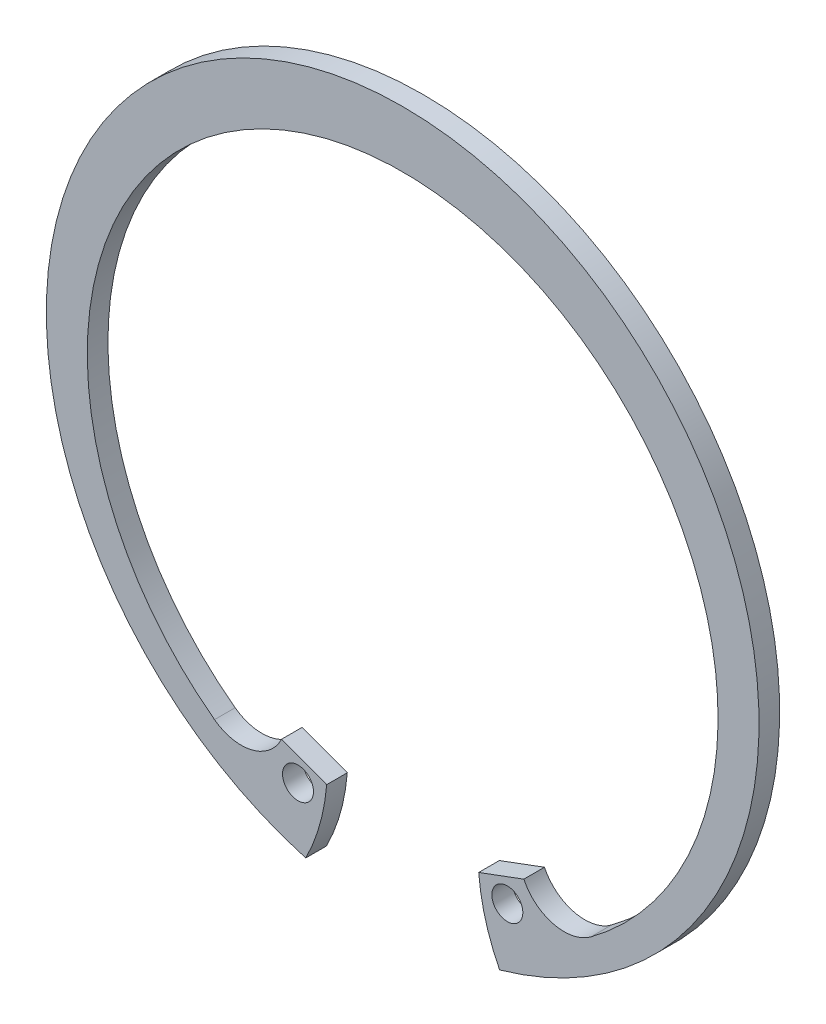
SolidWorks part; units mm, degrees
ref_plane "Front Plane" through (0, 0, 0) normal (0, 0, 1) x (1, 0, 0)
ref_plane "Top Plane" through (0, 0, 0) normal (0, 1, 0) x (1, 0, 0)
ref_plane "Right Plane" through (0, 0, 0) normal (1, 0, 0) x (0, 0, -1)
sketch "Sketch1" plane through (0, 0, 0) normal (0, 0, 1) x (1, 0, 0)
  line L0 (0, 27.1907) -> (0, 22.8727) construction
  line L1 (-15.5959, -22.2733) -> (-14.3576, -20.5048) construction
  line L2 (0, 0) -> (0, -27.1907) construction
  line L3 (-5.5626, -20.6113) -> (-7.0848, -26.2515) construction
  line L4 (-5.5626, -20.6113) -> (-7.9248, -20.6113) construction
  circle A0 centre (0, 0) radius 26.1112 construction
  circle A1 centre (0, 0) radius 27.1907 construction
  circle A2 centre (0, 0) radius 24.6062 construction
  dimension "Ring OD" = 54.3814
  dimension "For ID" = 49.2125
  dimension "Maximum Section" = 4.318
  dimension "D1" = 145
  dimension "Minimum Section" = 2.159
  dimension "Gap Width" = 11.1252
  dimension "Lug Height" = 5.842
  dimension "Hole Diameter" = 2.3622
sketch "Sketch2" plane through (0, 0, 0) normal (1, 0, 0) x (0, 0, -1)
  line L0 (-0.8636, 27.1907) -> (0.8636, 27.1907) construction
  line L1 (-0.7874, -27.1907) -> (0.7874, -27.1907) construction
  point P3 (0, 27.1907)
  point P7 (0, -27.1907)
  point P8 (-0.7874, -27.1907)
  point P10 (0.7874, -27.1907)
  point P11 (-0.8636, 27.1907)
  point P12 (0.8636, 27.1907)
  dimension "For Groove Width" = 1.7272
  dimension "Ring Thickness" = 1.5748
sketch "Sketch3" plane through (0, 0, 0) normal (0, 0, 1) x (1, 0, 0)
  line L0 (-7.0848, -26.2515) -> (-5.5626, -20.6113)
  line L1 (-5.5626, -20.6113) -> (-9.2442, -19.2435)
  line L2 (0, 0) -> (-7.4034, -19.9274) construction
  line L3 (-14.3576, -20.5048) -> (14.3576, -20.5048) construction
  line L4 (0, 0) -> (0, -27.1907) construction
  line L5 (-9.2442, -19.2435) -> (0, 0) construction
  line L6 (-7.4034, -19.9274) -> (-7.9864, -21.4966) construction
  line L7 (-7.9864, -21.4966) -> (-8.5694, -23.0658) construction
  line L8 (0, 27.1907) -> (0, 22.8727) construction
  line L9 (5.5626, -20.6113) -> (9.2442, -19.2435)
  line L10 (7.0848, -26.2515) -> (5.5626, -20.6113)
  arc A0 (-7.0848, -26.2515) -> (7.0848, -26.2515) centre (0, 0) cw
  circle A1 centre (0, 0) radius 27.1907 construction
  arc A2 (-14.3576, -20.5048) -> (14.3576, -20.5048) centre (0, -1.1922) cw
  arc A3 (-14.3576, -20.5048) -> (-9.2442, -19.2435) centre (-12.3211, -17.7654) ccw
  circle A4 centre (-7.9864, -21.4966) radius 1.1811
  circle A5 centre (0, 0) radius 25.0317 construction
  arc A6 (14.3576, -20.5048) -> (9.2442, -19.2435) centre (12.3211, -17.7654) cw
  circle A7 centre (7.9864, -21.4966) radius 1.1811
  circle A8 centre (0, 0) radius 24.6063 construction
  point P3 (0, -20.5048)
  dimension "D1" = 2.3622
extrude "Boss-Extrude1" add sketch "Sketch3" against normal up to vertex (0.7874 mm away) and the other way up to vertex (0.7874 mm away) up to point (0, -27.1907, -0.7874) other way up to point (0, -27.1907, 0.7874)
sketch "Sketch4" plane through (0, 0, 0) normal (0, 0, 1) x (1, 0, 0)
  line L0 (-5.5626, -20.6113) -> (-9.2442, -19.2435) construction
  line L1 (-5.5626, -20.6113) -> (-7.0848, -26.2515) construction
  line L2 (-7.3956, -26.1656) -> (-5.8007, -20.5228) construction
  line L3 (-5.8007, -20.5228) -> (0, 0) construction
  line L4 (-7.3956, -26.1656) -> (-7.3956, -33.5612)
  line L5 (-7.3956, -33.5612) -> (0, -33.5612)
  line L6 (0, -33.5612) -> (0, -27.1907)
  line L7 (0, -27.1907) -> (0, -20.5228)
  line L8 (0, 0) -> (0, -27.1907) construction
  line L9 (0, -20.5228) -> (-5.8007, -20.5228)
  arc A0 (-5.8007, -20.5228) -> (-7.3956, -26.1656) centre (-20.8893, -19.3049) cw
  circle A1 centre (0, 0) radius 27.1907 construction
  dimension "D1" = 0.254
extrude "Cut-Extrude1" cut sketch "Sketch4" against normal through all both and the other way through all
mirror "Mirror1" about plane through (0, 0, 0) normal (1, 0, 0) of "Cut-Extrude1"
equation "\"D1@Sketch3\"=\"Hole Diameter@Sketch1\""
